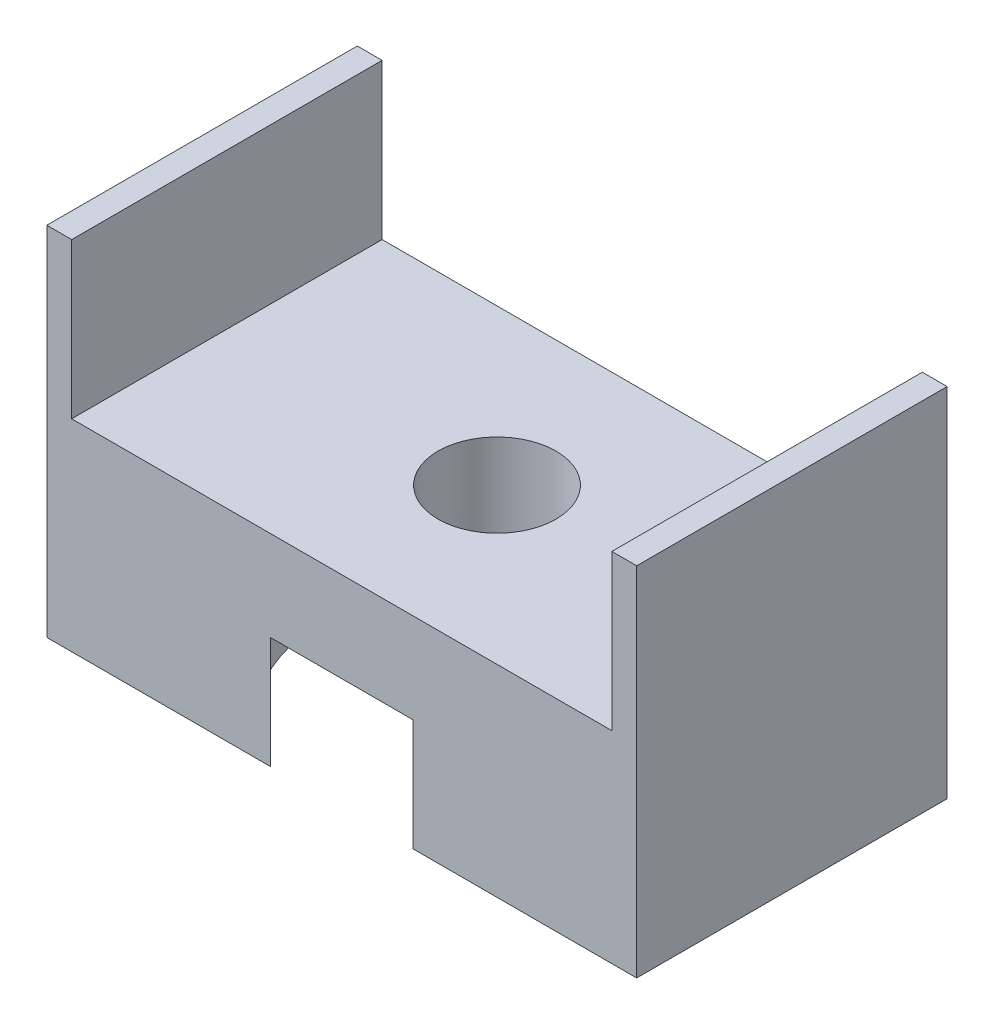
SolidWorks part; units mm, degrees
ref_plane "Front Plane" through (0, 0, 0) normal (0, 0, 1) x (1, 0, 0)
ref_plane "Top Plane" through (0, 0, 0) normal (0, 1, 0) x (1, 0, 0)
ref_plane "Right Plane" through (0, 0, 0) normal (1, 0, 0) x (0, 0, -1)
sketch "Sketch2" plane through (0, 0, 0) normal (0, 1, 0) x (1, 0, 0)
  line L1 (0.1589, 1.3651) -> (24.2889, 1.3651)
  line L2 (0.1589, 1.3651) -> (0.1589, 14.0651)
  line L3 (0.1589, 14.0651) -> (24.2889, 14.0651)
  line L4 (24.2889, 1.3651) -> (24.2889, 14.0651)
  circle A0 centre (12.2239, 7.7151) radius 2.413
  dimension "D3" = 6.35
  dimension "D5" = 4.826
  dimension "D1" = 12.7
  dimension "D2" = 24.13
  dimension "D4" = 12.065
extrude "Boss-Extrude1" add sketch "Sketch2" along normal blind 8.255
sketch "Sketch3" plane through (0, 8.255, 0) normal (0, 1, 0) x (1, 0, 0)
  line L0 (24.2889, 14.0651) -> (0.1589, 14.0651) construction
  line L1 (0.1589, 14.0651) -> (1.1749, 14.0651)
  line L2 (0.1589, 14.0651) -> (0.1589, 1.3651)
  line L3 (0.1589, 1.3651) -> (1.1749, 1.3651)
  line L4 (1.1749, 14.0651) -> (1.1749, 1.3651)
  line L5 (0.1589, 1.3651) -> (24.2889, 1.3651) construction
  line L6 (0.1589, 14.0651) -> (0.1589, 1.3651) construction
  dimension "D1" = 1.016
  dimension "D2" = 0
  dimension "D3" = 0
  dimension "D4" = 0
extrude "Boss-Extrude2" add sketch "Sketch3" along normal blind 6.35
sketch "Sketch4" plane through (0, 0, 0) normal (0, -1, 0) x (1, 0, 0)
  circle A3 centre (12.2239, -7.7151) radius 6.985
  circle A4 centre (12.2239, -7.7151) radius 6.985
  dimension "D1" = 4.572
extrude "Cut-Extrude1" cut sketch "Sketch4" against normal blind 4.572
sketch "Sketch5" plane through (0, 8.255, 0) normal (0, 1, 0) x (1, 0, 0)
  line L0 (24.2889, 1.3651) -> (24.2889, 14.0651) construction
  line L1 (24.2889, 14.0651) -> (23.2729, 14.0651)
  line L2 (24.2889, 14.0651) -> (24.2889, 1.3651)
  line L3 (24.2889, 1.3651) -> (23.2729, 1.3651)
  line L4 (23.2729, 14.0651) -> (23.2729, 1.3651)
  line L5 (1.1749, 1.3651) -> (24.2889, 1.3651) construction
  line L6 (24.2889, 14.0651) -> (1.1749, 14.0651) construction
  dimension "D1" = 1.016
  dimension "D2" = 0
  dimension "D3" = 0
  dimension "D4" = 0
extrude "Boss-Extrude3" add sketch "Sketch5" along normal blind 6.35
